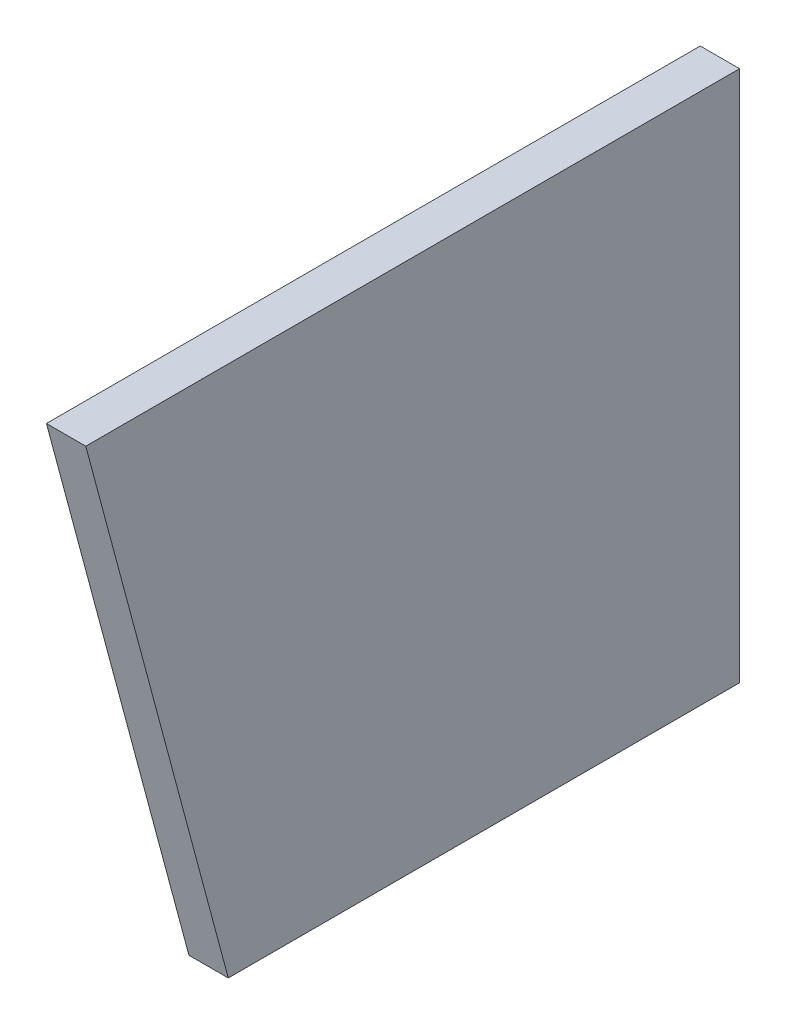
SolidWorks part; units mm, degrees
material "Cedar"
ref_plane "Front Plane" through (0, 0, 0) normal (0, 0, 1) x (1, 0, 0)
ref_plane "Top Plane" through (0, 0, 0) normal (0, 1, 0) x (1, 0, 0)
ref_plane "Right Plane" through (0, 0, 0) normal (1, 0, 0) x (0, 0, -1)
ref_plane "Plane1" through (0, 0, 0) normal (0.7071, 0, 0.7071) x (0.7071, 0, -0.7071)
sketch "Sketch2" plane through (0, 0, 0) normal (0, 0, 1) x (1, 0, 0)
  line L0 (-12.7, 0) -> (0, 0)
  line L1 (0, 0) -> (0, 171.7294)
  line L2 (0, 171.7294) -> (-12.7, 171.7294)
  line L3 (-12.7, 171.7294) -> (-12.7, 0)
  line L4 (0, 0) -> (-12.7, 0) construction
  line L5 (-12.7, 0) -> (-12.7, 177.6975) construction
  dimension "D1" = 0
  dimension "D2" = 12.7
  dimension "D3" = 171.7294
  dimension "D4" = 0
  dimension "D5" = 171.7294
extrude "Boss-Extrude2" add sketch "Sketch2" along normal blind 381
sketch "Sketch3" plane through (0, 0, 0) normal (1, 0, 0) x (0, 0, -1)
  line L0 (-165.1, 0) -> (-211.1148, 171.7294)
  line L1 (6.985, 0) -> (-6.985, 0) construction
  line L2 (-381, 171.7294) -> (0, 171.7294) construction
  line L3 (-211.1148, 171.7294) -> (-381, 171.7294)
  line L4 (-381, 171.7294) -> (-381, 0)
  line L5 (-381, 0) -> (-165.1, 0)
  line L6 (0, 6.985) -> (0, -6.985) construction
  line L7 (-165.1, 0) -> (-165.1, 171.7294) construction
  dimension "D1" = 165.1
  dimension "D2" = 15
extrude "Cut-Extrude1" cut sketch "Sketch3" against normal through all
